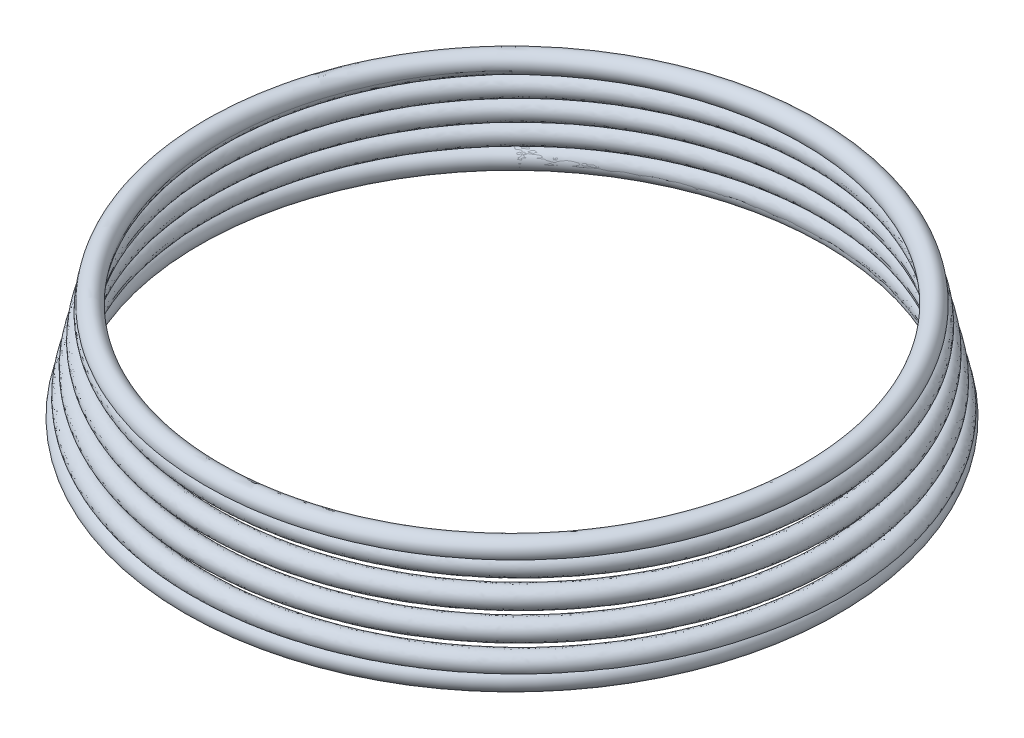
SolidWorks part; units mm, degrees
ref_plane "Alzado" through (0, 0, 0) normal (0, 0, 1) x (1, 0, 0)
ref_plane "Planta" through (0, 0, 0) normal (0, 1, 0) x (1, 0, 0)
ref_plane "Vista lateral" through (0, 0, 0) normal (1, 0, 0) x (0, 0, -1)
sketch "Croquis1" plane through (0, 0, 0) normal (0, 0, 1) x (1, 0, 0)
  line L0 (0, 0) -> (0, 2)
  circle A0 centre (5.55, 0) radius 0.175
  dimension "D1" = 0.35
  dimension "D2" = 5.55
  dimension "D3" = 2
sketch "Croquis2" plane through (0, 0, 0) normal (0, 1, 0) x (1, 0, 0)
  circle A0 centre (0, 0) radius 5.55
revolve "Revolución1" add sketch "Croquis1" angle 360 about L0
curve "Hélice/Espiral1"
sketch "Croquis3" plane through (0, 0, 0) normal (0, 1, 0) x (1, 0, 0)
  circle A0 centre (0, 0) radius 5.55
  dimension "D1" = 11.1
ref_plane "Plano1" through (-3.665, 1.7, -3.665) normal (0.709, 0.013, -0.7051) x (-0.701, -0.0955, -0.7067)
sketch "Croquis6" plane through (-3.665, 1.7, -3.665) normal (0.709, 0.013, -0.7051) x (-0.701, -0.0955, -0.7067)
  circle A0 centre (0, 0) radius 0.175
  dimension "D1" = 0.35
sweep "Barrer1" add profiles "Croquis6" path "Hélice/Espiral1"
ref_point "Punto1"
ref_plane "Plano3" through (0, 0, 0) normal (-0.7071, 0, 0.7071) x (0.7071, 0, 0.7071)
sketch "Croquis7" plane through (0, 0, 0) normal (-0.7071, 0, 0.7071) x (0.7071, 0, 0.7071)
  line L0 (0, 0) -> (0, 1.7)
  circle A0 centre (-5.1831, 1.7) radius 0.175
  dimension "D1" = 0.35
revolve "Revolución2" add sketch "Croquis7" angle 360 about L0
